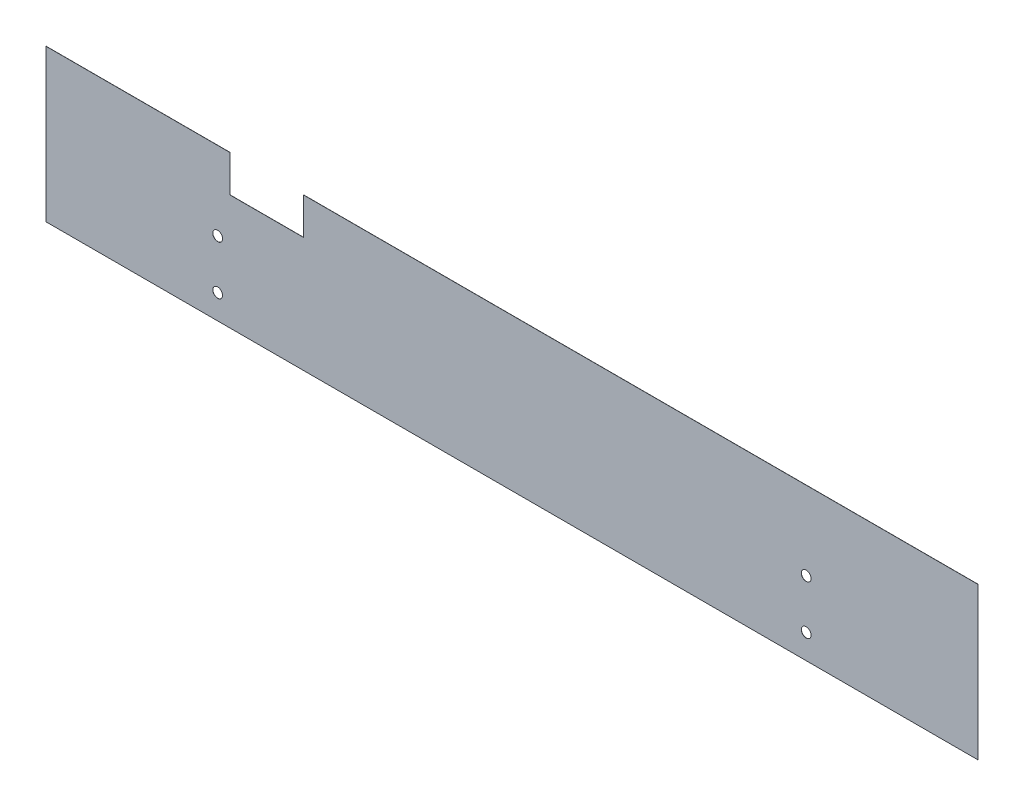
SolidWorks part; units mm, degrees
ref_plane "Front Plane" through (0, 0, 0) normal (0, 0, 1) x (1, 0, 0)
ref_plane "Top Plane" through (0, 0, 0) normal (0, 1, 0) x (1, 0, 0)
ref_plane "Right Plane" through (0, 0, 0) normal (1, 0, 0) x (0, 0, -1)
sketch "Sketch1" plane through (0, 0, 0) normal (0, 0, 1) x (1, 0, 0)
  line L1 (-190, -31) -> (190, -31)
  line L2 (-190, -31) -> (-190, 31)
  line L3 (-190, 31) -> (190, 31)
  line L4 (190, -31) -> (190, 31)
  line L5 (-190, -31) -> (190, 31) construction
  line L6 (-190, 31) -> (190, -31) construction
  point P0 (0, 0)
  dimension "D1" = 380
  dimension "D2" = 62
extrude "Body" add sketch "Sketch1" along normal blind 0.0625
sketch "Sketch2" plane through (0, 0, 0.0625) normal (0, 0, 1) x (1, 0, 0)
  line L0 (-120, -21) -> (120, -21) construction
  line L1 (120, -21) -> (120, -1) construction
  line L2 (120, -1) -> (-120, -1) construction
  line L3 (-120, -1) -> (-120, -21) construction
  line L4 (0, -1) -> (0, -21) construction
  line L6 (-190, -31) -> (190, -31) construction
  line L7 (-190, 31) -> (-190, -31) construction
  circle A0 centre (-120, -1) radius 2
  circle A1 centre (120, -1) radius 2
  circle A2 centre (120, -21) radius 2
  circle A3 centre (-120, -21) radius 2
  dimension "D1" = 4
  dimension "D2" = 20
  dimension "D3" = 10
  dimension "D4" = 70
extrude "Magnetic Holder" cut sketch "Sketch2" against normal blind 0.0625
sketch "Sketch3" plane through (0, 0, 0.0625) normal (0, 0, 1) x (1, 0, 0)
  line L0 (190, 31) -> (-190, 31) construction
  line L1 (-115, 31) -> (-85, 31)
  line L2 (-115, 31) -> (-115, 16)
  line L3 (-115, 16) -> (-85, 16)
  line L4 (-85, 31) -> (-85, 16)
  line L5 (-190, 31) -> (-190, -31) construction
  dimension "D1" = 75
  dimension "D2" = 30
  dimension "D3" = 15
extrude "Cut-Extrude2" cut sketch "Sketch3" against normal blind 0.0625
